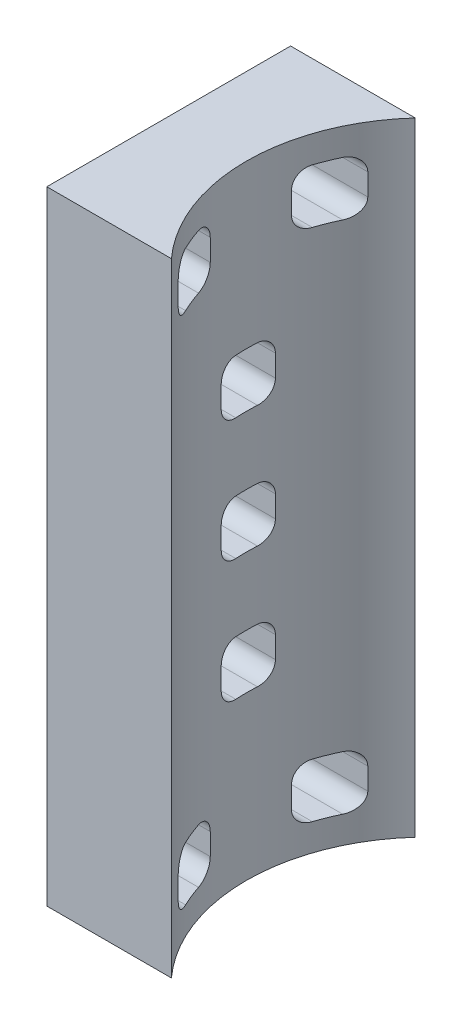
SolidWorks part; units mm, degrees
ref_plane "Front Plane" through (0, 0, 0) normal (0, 0, 1) x (1, 0, 0)
ref_plane "Top Plane" through (0, 0, 0) normal (0, 1, 0) x (1, 0, 0)
ref_plane "Right Plane" through (0, 0, 0) normal (1, 0, 0) x (0, 0, -1)
sketch "Sketch1" plane through (0, 0, 0) normal (1, 0, 0) x (0, 0, -1)
  line L1 (-22.5, 57.5) -> (22.5, 57.5)
  line L2 (-22.5, 57.5) -> (-22.5, -57.5)
  line L3 (-22.5, -57.5) -> (22.5, -57.5)
  line L4 (22.5, 57.5) -> (22.5, -57.5)
  line L5 (-22.5, 57.5) -> (22.5, -57.5) construction
  line L6 (-22.5, -57.5) -> (22.5, 57.5) construction
  point P0 (0, 0)
  dimension "D1" = 115
  dimension "D2" = 45
extrude "Boss-Extrude1" add sketch "Sketch1" along normal blind 23
sketch "Sketch2" plane through (0, 57.5, 0) normal (0, 1, 0) x (1, 0, 0)
  circle A0 centre (47.8193, 0) radius 33.5
extrude "Cut-Extrude1" cut sketch "Sketch2" against normal blind 121
sketch "Sketch3" plane through (0, 0, 0) normal (-1, 0, 0) x (0, 0, 1)
  line L0 (22.5, 57.5) -> (22.5, -57.5) construction
  line L1 (17.5, -52.5) -> (7.5, -52.5)
  line L2 (17.5, -52.5) -> (17.5, -42.5)
  line L3 (17.5, -42.5) -> (7.5, -42.5)
  line L4 (7.5, -52.5) -> (7.5, -42.5)
  line L5 (-7.5, -52.5) -> (-17.5, -52.5)
  line L6 (-7.5, -52.5) -> (-7.5, -42.5)
  line L7 (-7.5, -42.5) -> (-17.5, -42.5)
  line L8 (-17.5, -52.5) -> (-17.5, -42.5)
  line L9 (5, -27.5) -> (-5, -27.5)
  line L10 (5, -27.5) -> (5, -17.5)
  line L11 (5, -17.5) -> (-5, -17.5)
  line L12 (-5, -27.5) -> (-5, -17.5)
  line L13 (5, -5) -> (-5, -5)
  line L14 (5, -5) -> (5, 5)
  line L15 (5, 5) -> (-5, 5)
  line L16 (-5, -5) -> (-5, 5)
  line L17 (5, 17.5) -> (-5, 17.5)
  line L18 (5, 17.5) -> (5, 27.5)
  line L19 (5, 27.5) -> (-5, 27.5)
  line L20 (-5, 17.5) -> (-5, 27.5)
  line L21 (17.5, 42.5) -> (7.5, 42.5)
  line L22 (17.5, 42.5) -> (17.5, 52.5)
  line L23 (17.5, 52.5) -> (7.5, 52.5)
  line L24 (7.5, 42.5) -> (7.5, 52.5)
  line L25 (-22.5, -57.5) -> (-22.5, 57.5) construction
  line L26 (22.5, -57.5) -> (-22.5, -57.5) construction
  line L27 (-22.5, 57.5) -> (22.5, 57.5) construction
  line L28 (-7.5, 42.5) -> (-17.5, 42.5)
  line L29 (-7.5, 42.5) -> (-7.5, 52.5)
  line L30 (-7.5, 52.5) -> (-17.5, 52.5)
  line L31 (-17.5, 42.5) -> (-17.5, 52.5)
  point P24 (17.5, -47.5)
  point P31 (0, -57.5)
  dimension "D1" = 10
  dimension "D2" = 10
  dimension "D3" = 5
  dimension "D4" = 5
  dimension "D5" = 5
  dimension "D6" = 5
  dimension "D7" = 10
  dimension "D8" = 10
  dimension "D9" = 10
  dimension "D10" = 10
  dimension "D11" = 17.5
  dimension "D12" = 10
  dimension "D13" = 10
  dimension "D14" = 17.5
  dimension "D15" = 30
  dimension "D16" = 52.5
  dimension "D17" = 10
  dimension "D18" = 10
  dimension "D19" = 10
  dimension "D20" = 10
  dimension "D21" = 17.5
  dimension "D22" = 5
  dimension "D23" = 10
  dimension "D24" = 10
  dimension "D25" = 5
  dimension "D26" = 5
  dimension "D27" = 5
  dimension "D28" = 30
extrude "Cut-Extrude3" cut sketch "Sketch3" against normal blind 31
fillet "Fillet2" radius 3 27 edges at (7.5848, -42.5, -7.5) (9.6268, -42.5, 17.5) (7.3473, -17.5, 5) (7.3473, 5, 5) (7.3473, 27.5, 5) (7.5848, 52.5, -7.5) (9.6268, 52.5, 17.5) (7.5848, -42.5, 7.5) (9.6268, -42.5, -17.5) (7.3473, -17.5, -5) (7.3473, 5, -5) (7.3473, 27.5, -5) (9.6268, 52.5, -17.5) (7.5848, 52.5, 7.5) (9.6268, -52.5, -17.5) (7.3473, -27.5, -5) (7.3473, -5, -5) (7.3473, 17.5, -5) (9.6268, 42.5, -17.5) (7.5848, 42.5, 7.5) (7.5848, -52.5, -7.5) (9.6268, -52.5, 17.5) (7.3473, -27.5, 5) (7.3473, -5, 5) (7.3473, 17.5, 5) (9.6268, 42.5, 17.5) (7.5848, 42.5, -7.5)
fillet "Fillet3" radius 3 1 edges at (7.5848, -52.5, 7.5)
sketch "Sketch5" plane through (0, 0, 0) normal (-1, 0, 0) x (0, 0, 1)
  line L0 (2, -17.5) -> (-2, -17.5) construction
  line L1 (0.75, -17.5) -> (-0.75, -17.5)
  line L2 (0.75, -17.5) -> (0.75, -5)
  line L3 (0.75, -5) -> (-0.75, -5)
  line L4 (-0.75, -17.5) -> (-0.75, -5)
  line L5 (-2, -5) -> (2, -5) construction
  line L6 (2, 5) -> (-2, 5) construction
  line L7 (0.75, 5) -> (-0.75, 5)
  line L8 (0.75, 5) -> (0.75, 17.5)
  line L9 (0.75, 17.5) -> (-0.75, 17.5)
  line L10 (-0.75, 5) -> (-0.75, 17.5)
  line L11 (-2, 17.5) -> (2, 17.5) construction
  line L12 (2, 27.5) -> (-2, 27.5) construction
  line L13 (0.75, 27.5) -> (-0.75, 27.5)
  line L14 (0.75, 27.5) -> (0.75, 46.75)
  line L15 (0.75, 46.75) -> (-0.75, 46.75)
  line L16 (-0.75, 27.5) -> (-0.75, 46.75)
  line L17 (7.5, 49.5) -> (7.5, 45.5) construction
  line L18 (7.5, 46.75) -> (-7.5, 46.75)
  line L19 (7.5, 46.75) -> (7.5, 48.25)
  line L20 (7.5, 48.25) -> (-7.5, 48.25)
  line L21 (-7.5, 46.75) -> (-7.5, 48.25)
  line L22 (-7.5, 45.5) -> (-7.5, 49.5) construction
  line L23 (7.5, -45.5) -> (7.5, -49.5) construction
  line L24 (7.5, -48.25) -> (-7.5, -48.25)
  line L25 (7.5, -48.25) -> (7.5, -46.75)
  line L26 (7.5, -46.75) -> (-7.5, -46.75)
  line L27 (-7.5, -48.25) -> (-7.5, -46.75)
  line L28 (-7.5, -49.5) -> (-7.5, -45.5) construction
  line L29 (-2, -27.5) -> (2, -27.5) construction
  line L30 (0.75, -27.5) -> (-0.75, -27.5)
  line L31 (0.75, -27.5) -> (0.75, -46.75)
  line L32 (0.75, -46.75) -> (-0.75, -46.75)
  line L33 (-0.75, -27.5) -> (-0.75, -46.75)
  line L34 (10.5, -52.5) -> (14.5, -52.5) construction
  line L35 (14.5, -42.5) -> (10.5, -42.5) construction
  line L37 (-5, -20.5) -> (-5, -24.5) construction
  line L38 (5, -24.5) -> (5, -20.5) construction
  line L39 (-5, 2) -> (-5, -2) construction
  line L40 (5, -2) -> (5, 2) construction
  line L41 (5, 20.5) -> (5, 24.5) construction
  line L42 (-5, 24.5) -> (-5, 20.5) construction
  line L43 (10.5, 42.5) -> (14.5, 42.5) construction
  line L44 (14.5, 52.5) -> (10.5, 52.5) construction
  point P64 (0.75, 46.75)
  point P65 (0.75, -46.75)
  point P66 (0.75, -46.75)
  point P67 (0.75, -46.75)
  dimension "D1" = 4.25
  dimension "D2" = 4.25
  dimension "D3" = 6.75
  dimension "D4" = 6.75
  dimension "D5" = 4.25
  dimension "D6" = 4.25
  dimension "D7" = 4.25
  dimension "D8" = 4.25
  dimension "D9" = 4.25
  dimension "D10" = 4.25
  dimension "D11" = 4.25
  dimension "D12" = 4.25
extrude "Cut-Extrude4" cut sketch "Sketch5" against normal blind 3 contours L27 L24 L25 L26 | L2 L3 L4 L1 | L31 L32 L33 L30 | L10 L9 L8 L7 | L14 L15 L16 L13 | L18 L21 L20 L19
